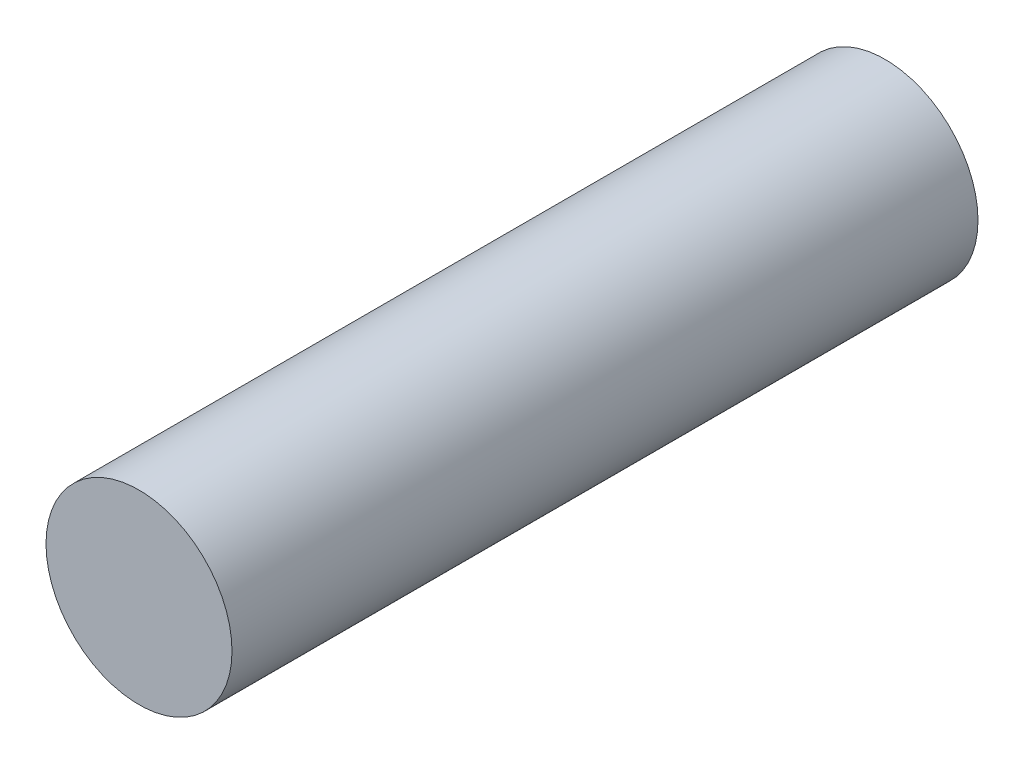
SolidWorks part; units mm, degrees
material "Plain Carbon Steel"
ref_plane "Front Plane" through (0, 0, 0) normal (0, 0, 1) x (1, 0, 0)
ref_plane "Top Plane" through (0, 0, 0) normal (0, 1, 0) x (1, 0, 0)
ref_plane "Right Plane" through (0, 0, 0) normal (1, 0, 0) x (0, 0, -1)
sketch "Sketch1" plane through (0, 0, 0) normal (0, 0, 1) x (1, 0, 0)
  circle A0 centre (0, 0) radius 2.3749
  dimension "D1" = 4.7498
extrude "Boss-Extrude1" add sketch "Sketch1" against normal blind 19.05
